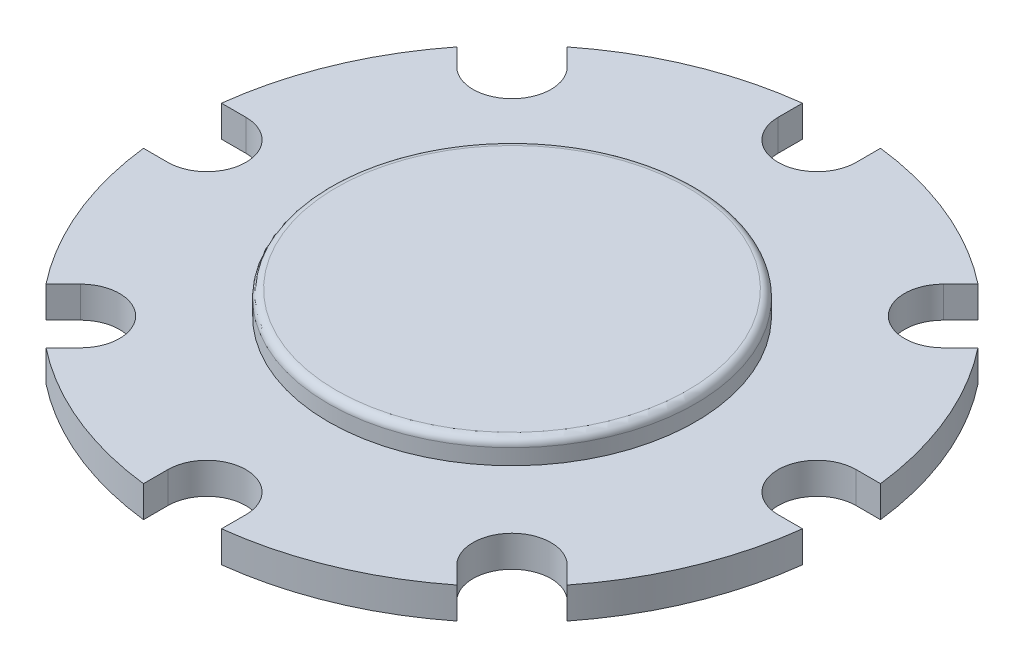
SolidWorks part; units mm, degrees
ref_plane "Front Plane" through (0, 0, 0) normal (0, 0, 1) x (1, 0, 0)
ref_plane "Top Plane" through (0, 0, 0) normal (0, 1, 0) x (1, 0, 0)
ref_plane "Right Plane" through (0, 0, 0) normal (1, 0, 0) x (0, 0, -1)
sketch "Sketch1" plane through (0, 0, 0) normal (0, 1, 0) x (1, 0, 0)
  circle A0 centre (0, 0) radius 21.25
  dimension "D1" = 42.5
extrude "Boss-Extrude1" add sketch "Sketch1" along normal blind 2
sketch "Sketch2" plane through (0, 2, 0) normal (0, 1, 0) x (1, 0, 0)
  circle A0 centre (0, 0) radius 11.75
  dimension "D1" = 23.5
extrude "Boss-Extrude2" add sketch "Sketch2" along normal blind 1.5
fillet "Fillet1" radius 0.5 1 edges at (0, 3.5, 11.75)
sketch "Sketch3" plane through (0, 0, 0) normal (0, -1, 0) x (1, 0, 0)
  line L0 (0, 25.3011) -> (0, -22.461) construction
  line L1 (-3, 25.3011) -> (-3, 17.0611) construction
  line L2 (3, 25.3011) -> (3, 16.7006) construction
  line L4 (-3, 23.2919) -> (3, 23.2919)
  line L5 (-3, 23.2919) -> (-3, 19.2919)
  line L6 (-3, 19.2919) -> (3, 19.2919)
  line L7 (3, 23.2919) -> (3, 19.2919)
  circle A1 centre (0, 0) radius 21.25 construction
  dimension "D1" = 3
  dimension "D2" = 3
  dimension "D3" = 4
  dimension "D4" = 23.2919
extrude "Cut-Extrude1" [suppressed] cut sketch "Sketch3" against normal through all
fillet "Fillet2" [suppressed] radius 2
sketch "Sketch4" plane through (0, 0, 0) normal (0, -1, 0) x (1, 0, 0)
  line L0 (-19.1049, 19.54) -> (23.13, 19.54) construction
  line L3 (-2.5, 19.54) -> (-2.5, 23.75)
  line L4 (-2.5, 23.75) -> (2.5, 23.75)
  line L5 (2.5, 19.54) -> (2.5, 23.75)
  circle A0 centre (0, 0) radius 21.25 construction
  arc A1 (-2.5, 19.54) -> (2.5, 19.54) centre (0, 19.54) ccw
  point P2 (0, 21.25)
  dimension "D1" = 1.71
extrude "Cut-Extrude2" cut sketch "Sketch4" against normal through all
sketch "Sketch5" plane through (0, 0, 0) normal (0, -1, 0) x (-1, 0, 0)
  line L0 (21.25, 0) -> (-21.25, 0) construction
  line L1 (0, -21.3042) -> (0, 21.25) construction
  circle A0 centre (0, 0) radius 1.6544
  arc A1 (2.5, -21.1024) -> (-2.5, -21.1024) centre (0, 0) ccw construction
extrude "Cut-Extrude3" cut sketch "Sketch5" against normal blind 0.01 contours A0
pattern_circular "CirPattern1" count 8 over 360 about axis through (0, 0, 0) along (0, 1, 0) of "Cut-Extrude2"
